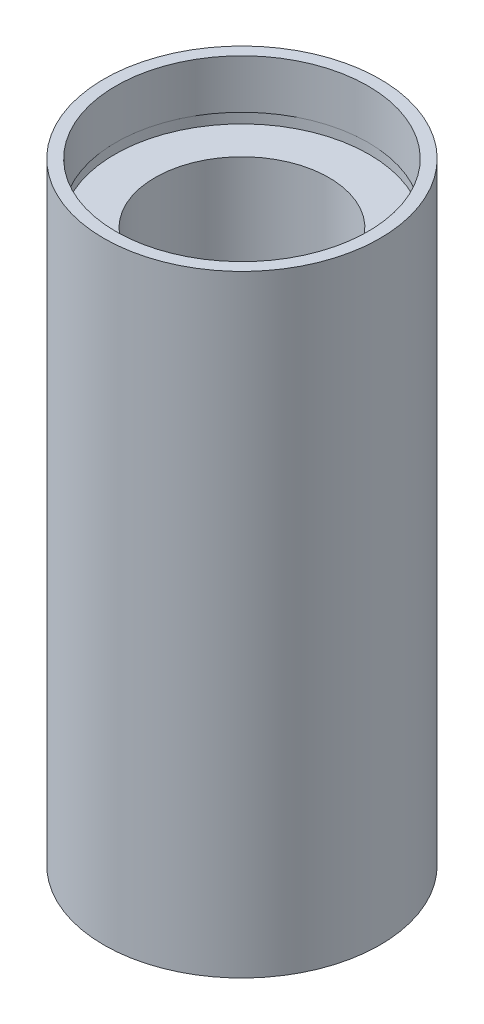
SolidWorks part; units mm, degrees
ref_plane "前视基准面" through (0, 0, 0) normal (0, 0, 1) x (1, 0, 0)
ref_plane "上视基准面" through (0, 0, 0) normal (0, 1, 0) x (1, 0, 0)
ref_plane "右视基准面" through (0, 0, 0) normal (1, 0, 0) x (0, 0, -1)
sketch "草图1" plane through (0, 0, 0) normal (0, 0, 1) x (1, 0, 0)
  line L0 (0, 161.3762) -> (0, 0) construction
  line L1 (141.7365, 0) -> (-131.7984, 0) construction
  line L2 (11.1, 0) -> (11.1, 4.5)
  line L3 (11.7, 4.5) -> (11.7, 5.5)
  line L4 (11.1, 4.5) -> (11.7, 4.5)
  line L5 (8, 5.5) -> (8, 50.8)
  line L6 (11.7, 5.5) -> (8, 5.5)
  line L7 (12.7, 0) -> (12.7, 56.3)
  line L8 (11.1, 0) -> (12.7, 0)
  line L9 (11.6, 56.3) -> (11.6, 51.8)
  line L10 (11.6, 56.3) -> (12.7, 56.3)
  line L11 (11.7, 51.8) -> (11.7, 50.8)
  line L12 (11.6, 51.8) -> (11.7, 51.8)
  line L13 (8, 50.8) -> (11.7, 50.8)
  point P15 (11.6, 54.05)
  dimension "D1" = 11.1
  dimension "D2" = 4.5
  dimension "D3" = 11.7
  dimension "D4" = 8
  dimension "D5" = 12.7
  dimension "D6" = 11.6
  dimension "D7" = 4.5
  dimension "D8" = 11.7
  dimension "D9" = 5.5
  dimension "D10" = 1
  dimension "D11" = 50.8
revolve "旋转1" add sketch "草图1" angle 360 about L0
cosmetic thread "装饰螺纹线1" parameters "D2"=23.2
cosmetic thread "装饰螺纹线2" parameters "D2"=17
cosmetic thread "装饰螺纹线3" parameters "D2"=23.21
